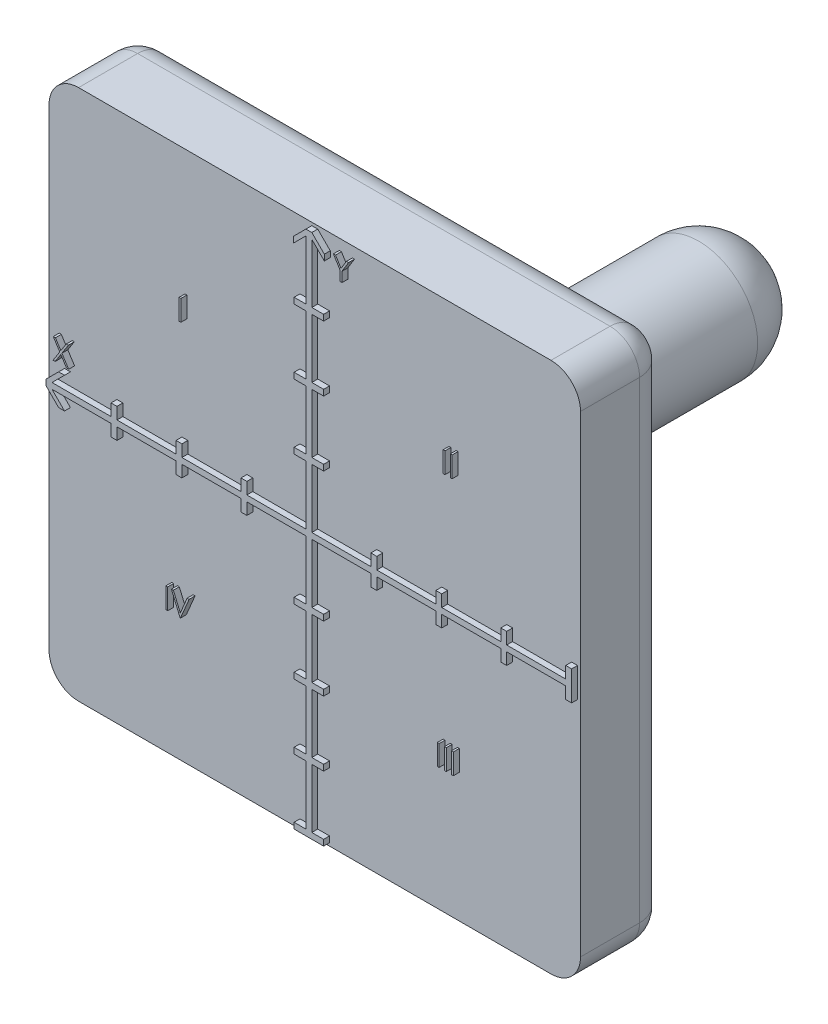
SolidWorks part; units mm, degrees
ref_plane "Alzado" through (0, 0, 0) normal (0, 0, 1) x (1, 0, 0)
ref_plane "Planta" through (0, 0, 0) normal (0, 1, 0) x (1, 0, 0)
ref_plane "Vista lateral" through (0, 0, 0) normal (1, 0, 0) x (0, 0, -1)
sketch "Croquis1" plane through (0, 0, 0) normal (0, 0, 1) x (1, 0, 0)
  line L1 (-45, -45) -> (45, -45)
  line L2 (-45, -45) -> (-45, 45)
  line L3 (-45, 45) -> (45, 45)
  line L4 (45, -45) -> (45, 45)
  line L5 (-45, -45) -> (45, 45) construction
  line L6 (-45, 45) -> (45, -45) construction
  point P0 (0, 0)
  dimension "D1" = 90
  dimension "D2" = 90
extrude "Saliente-Extruir2" add sketch "Croquis1" along normal blind 15
sketch "Croquis2" plane through (0, 0, 0) normal (0, 0, -1) x (-1, 0, 0)
  circle A0 centre (0, 0) radius 10
extrude "Saliente-Extruir3" add sketch "Croquis2" along normal blind 60
sketch "Croquis3" plane through (0, 0, 15) normal (0, 0, 1) x (1, 0, 0)
  line L14 (10.5, 0.5) -> (10.5, 2.5)
  line L15 (10.5, 2.5) -> (11.5, 2.5)
  line L16 (11.5, 2.5) -> (11.5, 0.5)
  line L18 (21.5, 0.5) -> (21.5, 2.5)
  line L19 (21.5, 2.5) -> (22.5, 2.5)
  line L20 (22.5, 2.5) -> (22.5, 0.5)
  line L22 (32.5, 0.5) -> (32.5, 2.5)
  line L23 (32.5, 2.5) -> (33.5, 2.5)
  line L24 (33.5, 2.5) -> (33.5, 0.5)
  line L25 (43.5, 0.5) -> (41.3787, 2.6213)
  line L26 (41.3787, 2.6213) -> (42.3787, 2.6213)
  line L27 (42.3787, 2.6213) -> (44.5, 0.5)
  line L28 (0, -41.25) -> (0, 41.25) construction
  line L29 (-42.3787, 2.6213) -> (-44.5, 0.5)
  line L30 (-41.3787, 2.6213) -> (-42.3787, 2.6213)
  line L31 (-43.5, 0.5) -> (-41.3787, 2.6213)
  line L32 (-33.5, 2.5) -> (-33.5, 0.5)
  line L33 (-32.5, 2.5) -> (-33.5, 2.5)
  line L34 (-32.5, 0.5) -> (-32.5, 2.5)
  line L35 (-22.5, 2.5) -> (-22.5, 0.5)
  line L36 (-21.5, 2.5) -> (-22.5, 2.5)
  line L37 (-21.5, 0.5) -> (-21.5, 2.5)
  line L38 (-11.5, 2.5) -> (-11.5, 0.5)
  line L39 (-10.5, 2.5) -> (-11.5, 2.5)
  line L40 (-10.5, 0.5) -> (-10.5, 2.5)
  line L45 (41.25, 0) -> (-41.25, 0) construction
  line L46 (42.3787, -2.6213) -> (44.5, -0.5)
  line L47 (41.3787, -2.6213) -> (42.3787, -2.6213)
  line L48 (43.5, -0.5) -> (41.3787, -2.6213)
  line L49 (33.5, -2.5) -> (33.5, -0.5)
  line L50 (32.5, -2.5) -> (33.5, -2.5)
  line L51 (32.5, -0.5) -> (32.5, -2.5)
  line L52 (22.5, -2.5) -> (22.5, -0.5)
  line L53 (21.5, -2.5) -> (22.5, -2.5)
  line L54 (21.5, -0.5) -> (21.5, -2.5)
  line L55 (11.5, -2.5) -> (11.5, -0.5)
  line L56 (10.5, -2.5) -> (11.5, -2.5)
  line L57 (10.5, -0.5) -> (10.5, -2.5)
  line L62 (-10.5, -0.5) -> (-10.5, -2.5)
  line L63 (-10.5, -2.5) -> (-11.5, -2.5)
  line L64 (-11.5, -2.5) -> (-11.5, -0.5)
  line L65 (-21.5, -0.5) -> (-21.5, -2.5)
  line L66 (-21.5, -2.5) -> (-22.5, -2.5)
  line L67 (-22.5, -2.5) -> (-22.5, -0.5)
  line L68 (-32.5, -0.5) -> (-32.5, -2.5)
  line L69 (-32.5, -2.5) -> (-33.5, -2.5)
  line L70 (-33.5, -2.5) -> (-33.5, -0.5)
  line L71 (-43.5, -0.5) -> (-41.3787, -2.6213)
  line L72 (-41.3787, -2.6213) -> (-42.3787, -2.6213)
  line L73 (-42.3787, -2.6213) -> (-44.5, -0.5)
  line L78 (-33.5, 0.5) -> (-43.5, 0.5)
  line L80 (-0.5, 10.5) -> (-2.5, 10.5)
  line L81 (-2.5, 10.5) -> (-2.5, 11.5)
  line L82 (-2.5, 11.5) -> (-0.5, 11.5)
  line L83 (-0.5, 21.5) -> (-2.5, 21.5)
  line L84 (-2.5, 21.5) -> (-2.5, 22.5)
  line L85 (-2.5, 22.5) -> (-0.5, 22.5)
  line L86 (-0.5, 32.5) -> (-2.5, 32.5)
  line L87 (-2.5, 32.5) -> (-2.5, 33.5)
  line L88 (-2.5, 33.5) -> (-0.5, 33.5)
  line L89 (-0.5, 43.5) -> (-2.6213, 41.3787)
  line L90 (-2.6213, 41.3787) -> (-2.6213, 42.3787)
  line L91 (-2.6213, 42.3787) -> (-0.5, 44.5)
  line L92 (-2.6213, -42.3787) -> (-0.5, -44.5)
  line L93 (-2.6213, -41.3787) -> (-2.6213, -42.3787)
  line L94 (-0.5, -43.5) -> (-2.6213, -41.3787)
  line L95 (-2.5, -33.5) -> (-0.5, -33.5)
  line L96 (-2.5, -32.5) -> (-2.5, -33.5)
  line L97 (-0.5, -32.5) -> (-2.5, -32.5)
  line L98 (-2.5, -22.5) -> (-0.5, -22.5)
  line L99 (-2.5, -21.5) -> (-2.5, -22.5)
  line L100 (-0.5, -21.5) -> (-2.5, -21.5)
  line L101 (-2.5, -11.5) -> (-0.5, -11.5)
  line L102 (-2.5, -10.5) -> (-2.5, -11.5)
  line L103 (-0.5, -10.5) -> (-2.5, -10.5)
  line L108 (2.6213, 42.3787) -> (0.5, 44.5)
  line L109 (2.6213, 41.3787) -> (2.6213, 42.3787)
  line L110 (0.5, 43.5) -> (2.6213, 41.3787)
  line L111 (2.5, 33.5) -> (0.5, 33.5)
  line L112 (2.5, 32.5) -> (2.5, 33.5)
  line L113 (0.5, 32.5) -> (2.5, 32.5)
  line L114 (2.5, 22.5) -> (0.5, 22.5)
  line L115 (2.5, 21.5) -> (2.5, 22.5)
  line L116 (0.5, 21.5) -> (2.5, 21.5)
  line L117 (2.5, 11.5) -> (0.5, 11.5)
  line L118 (2.5, 10.5) -> (2.5, 11.5)
  line L119 (0.5, 10.5) -> (2.5, 10.5)
  line L124 (0.5, -10.5) -> (2.5, -10.5)
  line L125 (2.5, -10.5) -> (2.5, -11.5)
  line L126 (2.5, -11.5) -> (0.5, -11.5)
  line L127 (0.5, -21.5) -> (2.5, -21.5)
  line L128 (2.5, -21.5) -> (2.5, -22.5)
  line L129 (2.5, -22.5) -> (0.5, -22.5)
  line L130 (0.5, -32.5) -> (2.5, -32.5)
  line L131 (2.5, -32.5) -> (2.5, -33.5)
  line L132 (2.5, -33.5) -> (0.5, -33.5)
  line L133 (0.5, -43.5) -> (2.6213, -41.3787)
  line L134 (2.6213, -41.3787) -> (2.6213, -42.3787)
  line L135 (2.6213, -42.3787) -> (0.5, -44.5)
  line L136 (-0.5, -32.5) -> (-0.5, -22.5)
  line L138 (0.5, 43.5) -> (0.5, 33.5)
  line L139 (-0.5, 44.5) -> (0.5, 44.5)
  line L140 (-0.5, -43.5) -> (-0.5, -33.5)
  line L141 (0.5, -33.5) -> (0.5, -43.5)
  line L142 (-0.5, -21.5) -> (-0.5, -11.5)
  line L143 (0.5, -22.5) -> (0.5, -32.5)
  line L144 (0.5, -11.5) -> (0.5, -21.5)
  line L145 (-0.5, -10.5) -> (-0.5, -0.5)
  line L146 (0.5, 10.5) -> (0.5, 0.5)
  line L147 (-0.5, 11.5) -> (-0.5, 21.5)
  line L148 (0.5, 21.5) -> (0.5, 11.5)
  line L149 (-0.5, 22.5) -> (-0.5, 32.5)
  line L150 (-0.5, 33.5) -> (-0.5, 43.5)
  line L151 (0.5, 32.5) -> (0.5, 22.5)
  line L152 (-44.5, 0.5) -> (-44.5, -0.5)
  line L153 (-33.5, -0.5) -> (-43.5, -0.5)
  line L154 (-22.5, 0.5) -> (-32.5, 0.5)
  line L155 (-22.5, -0.5) -> (-32.5, -0.5)
  line L156 (-11.5, 0.5) -> (-21.5, 0.5)
  line L157 (-11.5, -0.5) -> (-21.5, -0.5)
  line L158 (-0.5, -0.5) -> (-10.5, -0.5)
  line L159 (-0.5, 0.5) -> (-0.5, 10.5)
  line L160 (-0.5, -0.5) -> (-0.5, -10.5)
  line L161 (0.5, -0.5) -> (0.5, -10.5)
  line L162 (0.5, -0.5) -> (0.5, -10.5)
  line L163 (-0.5, 0.5) -> (-10.5, 0.5)
  line L164 (10.5, 0.5) -> (0.5, 0.5)
  line L165 (10.5, -0.5) -> (0.5, -0.5)
  line L166 (21.5, 0.5) -> (11.5, 0.5)
  line L167 (21.5, -0.5) -> (11.5, -0.5)
  line L168 (32.5, -0.5) -> (22.5, -0.5)
  line L169 (32.5, 0.5) -> (22.5, 0.5)
  line L170 (43.5, 0.5) -> (33.5, 0.5)
  line L171 (43.5, -0.5) -> (33.5, -0.5)
  line L172 (-0.5, 10.5) -> (-0.5, 0.5)
  line L173 (0.5, 10.5) -> (0.5, 0.5)
  line L174 (-0.5, 21.5) -> (-0.5, 11.5)
  line L175 (0.5, 21.5) -> (0.5, 11.5)
  line L176 (0.5, 32.5) -> (0.5, 22.5)
  line L177 (-0.5, 32.5) -> (-0.5, 22.5)
  line L178 (-0.5, 43.5) -> (-0.5, 33.5)
  line L179 (0.5, 43.5) -> (0.5, 33.5)
  line L182 (-0.5, -33.5) -> (-0.5, -43.5)
  line L183 (0.5, -33.5) -> (0.5, -43.5)
  line L184 (-0.5, -22.5) -> (-0.5, -32.5)
  line L185 (0.5, -22.5) -> (0.5, -32.5)
  line L186 (0.5, -11.5) -> (0.5, -21.5)
  line L187 (-0.5, -11.5) -> (-0.5, -21.5)
  line L188 (44.5, 0.5) -> (44.5, -0.5)
  line L189 (-0.5, -44.5) -> (0.5, -44.5)
  dimension "D6" = 1
  dimension "D8" = 1
  dimension "D9" = 10
  dimension "D10" = 1
  dimension "D12" = 10
  dimension "D13" = 1
  dimension "D14" = 1
  dimension "D16" = 10
extrude "Saliente-Extruir4" add sketch "Croquis3" along normal blind 1 contours L92 L189 L135 L134 L133 L141 L132 L131 L130 L143 L129 L128 L127 L144 L126 L125 L124 L161 L165 L57 L56 L55 L167 L54 L53 L52 L168 L51 L50 L49 L171 L48 L47 L46 L188 L27 L26 L25 L170 L24 L23 L22 L169 L20 L19 L18 L166 L16 L15 L14 L164
fillet "Redondeo1" radius 5 4 edges at (-45, -45, 7.5) (45, -45, 7.5) (-45, 45, 7.5) (45, 45, 7.5)
fillet "Redondeo2" radius 5 8 edges at (-43.5355, 43.5355, 0) (0, 45, 0) (43.5355, 43.5355, 0) (45, 0, 0) (43.5355, -43.5355, 0) (0, -45, 0) (-43.5355, -43.5355, 0) (-45, 0, 0)
fillet "Redondeo3" radius 5 1 edges at (-10, 0, 0)
fillet "Redondeo4" radius 10 1 edges at (-10, 0, -60)
sketch "Croquis4" plane through (0, 0, 15) normal (0, 0, 1) x (1, 0, 0)
  line L1 (44.5, -0.5) -> (43.5, -0.5)
  line L2 (42.3787, -2.6213) -> (44.5, -0.5)
  line L3 (41.3787, -2.6213) -> (42.3787, -2.6213)
  line L13 (2.6213, -41.3787) -> (2.6213, -42.3787)
  line L14 (2.6213, -41.3787) -> (2.6213, -42.3787) construction
  line L15 (2.6213, -42.3787) -> (0.5, -44.5)
  line L16 (0.5, -44.5) -> (0.5, -43.5)
  line L17 (0.5, -43.5) -> (2.6213, -41.3787) construction
  line L18 (0.5, -43.5) -> (2.6213, -41.3787) construction
  line L19 (0.5, -43.5) -> (2.6213, -41.3787)
  line L20 (-0.5, -44.5) -> (-0.5, -43.5)
  line L21 (-0.5, -43.5) -> (-2.6213, -41.3787)
  line L22 (-2.6213, -41.3787) -> (-2.6213, -42.3787)
  line L23 (-2.6213, -42.3787) -> (-0.5, -44.5)
  line L24 (43.5, -0.5) -> (41.3787, -2.6213)
  line L25 (42.3787, 2.6213) -> (44.5, 0.5)
  line L26 (41.3787, 2.6213) -> (42.3787, 2.6213)
  line L27 (43.5, 0.5) -> (41.3787, 2.6213)
  line L28 (44.5, 0.5) -> (43.5, 0.5)
sketch "Croquis6" plane through (0, 0, 15) normal (0, 0, 1) x (1, 0, 0)
  text T0 "X"
  text T1 "Y"
extrude "Cortar-Extruir3" cut sketch "Croquis4" along normal blind 7 contours L25 L28 L27 L26 | L1 L24 L3 L2 | L19 L13 L15 L16 | L23 L20 L21 L22
sketch "Croquis7" plane through (0, 0, 15) normal (0, 0, 1) x (1, 0, 0)
  line L1 (0.5, -44.5) -> (2.5, -44.5)
  line L2 (0.5, -44.5) -> (0.5, -43.5)
  line L3 (0.5, -43.5) -> (2.5, -43.5)
  line L4 (2.5, -44.5) -> (2.5, -43.5)
  line L5 (-0.5, -44.5) -> (-2.5, -44.5)
  line L6 (-0.5, -44.5) -> (-0.5, -43.5)
  line L7 (-0.5, -43.5) -> (-2.5, -43.5)
  line L8 (-2.5, -44.5) -> (-2.5, -43.5)
  line L9 (44.5, 0.5) -> (43.5, 0.5)
  line L10 (44.5, 0.5) -> (44.5, 2.5)
  line L11 (44.5, 2.5) -> (43.5, 2.5)
  line L12 (43.5, 0.5) -> (43.5, 2.5)
  line L13 (44.5, -0.5) -> (43.5, -0.5)
  line L14 (44.5, -0.5) -> (44.5, -2.5)
  line L15 (44.5, -2.5) -> (43.5, -2.5)
  line L16 (43.5, -0.5) -> (43.5, -2.5)
  dimension "D1" = 1
  dimension "D2" = 2
  dimension "D3" = 2
  dimension "D4" = 1
  dimension "D5" = 2
  dimension "D6" = 1
  dimension "D7" = 1
  dimension "D8" = 2
extrude "Saliente-Extruir7" add sketch "Croquis7" along normal blind 1
extrude "Saliente-Extruir8" add sketch "Croquis6" along normal blind 1
sketch "Croquis8" plane through (0, 0, 15) normal (0, 0, 1) x (1, 0, 0)
  text T0 "I"
  text T1 "II"
  text T2 "III"
  text T3 "IV"
extrude "Saliente-Extruir10" add sketch "Croquis8" along normal blind 1
